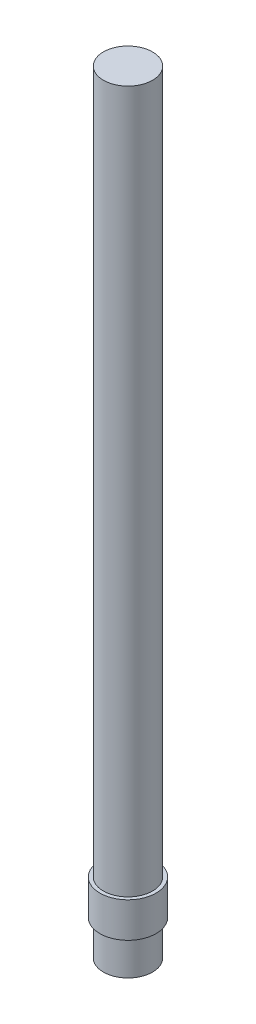
SolidWorks part; units mm, degrees
ref_plane "Front Plane" through (0, 0, 0) normal (0, 0, 1) x (1, 0, 0)
ref_plane "Top Plane" through (0, 0, 0) normal (0, 1, 0) x (1, 0, 0)
ref_plane "Right Plane" through (0, 0, 0) normal (1, 0, 0) x (0, 0, -1)
sketch "Sketch1" plane through (0, 0, 0) normal (0, 1, 0) x (1, 0, 0)
  circle A0 centre (0, 0) radius 3.5
  dimension "D1" = 7
extrude "Boss-Extrude1" add sketch "Sketch1" along normal blind 5
sketch "Sketch2" plane through (0, 5, 0) normal (0, 1, 0) x (1, 0, 0)
  circle A0 centre (0, 0) radius 4
  dimension "D1" = 8
extrude "Boss-Extrude2" add sketch "Sketch2" along normal blind 5
sketch "Sketch3" plane through (0, 10, 0) normal (0, 1, 0) x (1, 0, 0)
  circle A0 centre (0, 0) radius 3.5
  dimension "D1" = 7
extrude "Boss-Extrude3" add sketch "Sketch3" along normal blind 100
